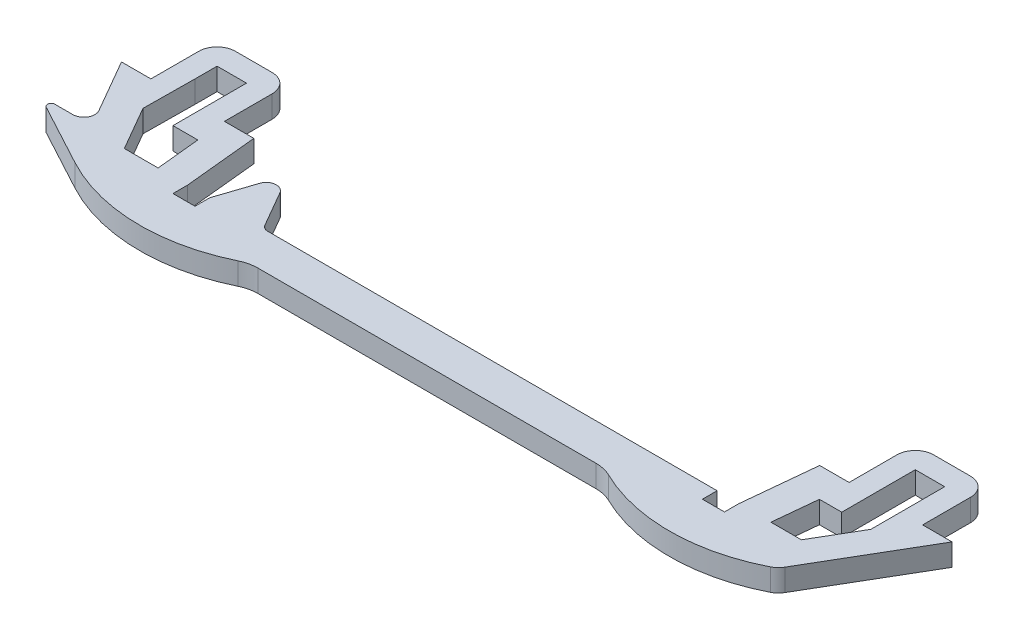
SolidWorks part; units mm, degrees
material "Custom Plastic"
ref_plane "Front Plane" through (0, 0, 0) normal (0, 0, 1) x (1, 0, 0)
ref_plane "Top Plane" through (0, 0, 0) normal (0, 1, 0) x (1, 0, 0)
ref_plane "Right Plane" through (0, 0, 0) normal (1, 0, 0) x (0, 0, -1)
sketch "Sketch1" plane through (0, 0, 0) normal (0, 1, 0) x (1, 0, 0)
  line L0 (-62.4186, -47.1375) -> (-58.4186, -47.1375)
  line L1 (-58.4186, -47.1375) -> (-58.4186, -38.1375)
  line L2 (-58.4186, -38.1375) -> (-48.4186, -38.1375)
  line L3 (-48.4186, -38.1375) -> (-48.4186, -47.1375)
  line L4 (-48.4186, -47.1375) -> (-44.4186, -47.1375)
  line L5 (-44.4186, -47.1375) -> (-43.4188, -57.135)
  line L7 (31.5814, -57.1876) -> (32.5814, -47.1902)
  line L8 (32.5814, -47.1902) -> (36.5814, -47.1902)
  line L9 (36.5814, -47.1902) -> (36.5814, -38.1902)
  line L10 (36.5814, -38.1902) -> (46.5814, -38.1902)
  line L11 (46.5814, -38.1902) -> (46.5814, -47.1902)
  line L12 (46.5814, -47.1902) -> (50.5814, -47.1902)
  line L13 (50.5814, -47.1902) -> (41.8306, -62.1375)
  line L15 (-58.2259, -54.3993) -> (-62.4186, -47.1375)
  line L16 (36.5478, -51.1902) -> (39.5814, -51.1902)
  line L17 (-55.4186, -41.1375) -> (-51.4186, -41.1375)
  line L18 (-55.4186, -41.1375) -> (-55.4186, -44.1379)
  line L20 (-51.4186, -41.1375) -> (-51.4186, -44.1375)
  line L21 (39.5814, -41.1902) -> (43.5814, -41.1902)
  line L22 (39.5814, -41.1902) -> (39.5814, -44.1902)
  line L24 (43.5814, -41.1902) -> (43.5814, -44.2297)
  line L25 (43.5814, -51.2297) -> (40.0934, -57.1876)
  line L26 (40.0934, -57.1876) -> (35.9479, -57.1876)
  line L27 (35.9479, -57.1876) -> (36.5478, -51.1902)
  line L28 (-51.4186, -51.1375) -> (-48.0385, -51.1375)
  line L29 (-48.0385, -51.1375) -> (-47.4385, -57.1375)
  line L30 (-47.4385, -57.1375) -> (-52.0263, -57.1375)
  line L31 (-52.0263, -57.1375) -> (-55.4904, -51.1375)
  line L32 (28.5814, -57.1375) -> (28.5814, -59.1375)
  line L33 (28.5814, -47.1587) -> (28.5814, -62.1587) construction
  line L34 (28.5814, -59.1375) -> (31.5814, -59.1375)
  line L35 (31.5814, -59.1375) -> (31.5814, -57.1876)
  line L36 (31.5814, -62.1587) -> (31.5814, -47.1587) construction
  line L38 (-43.4188, -57.135) -> (-43.4188, -59.1375)
  line L39 (-43.4188, -59.1375) -> (-40.4188, -59.1375)
  line L40 (-40.4188, -59.1375) -> (-40.4188, -57.1375)
  line L41 (-33.1369, -57.1375) -> (28.5814, -57.1375)
  line L42 (-33.1369, -57.1375) -> (-36.236, -51.7698)
  line L43 (43.5814, -44.2297) -> (43.5814, -51.2297)
  line L44 (-38.7227, -52.0235) -> (-40.4188, -57.1375)
  line L45 (39.5814, -44.1902) -> (39.5814, -51.1902)
  line L46 (-55.4186, -44.1379) -> (-55.4904, -51.1375)
  line L47 (-51.4186, -44.1375) -> (-51.4186, -51.1375)
  line L48 (-53.7583, -62.1375) -> (-62.2024, -57.5896)
  line L49 (-61.9653, -56.6493) -> (-59.525, -56.6493)
  line L50 (30.0814, -59.1375) -> (30.0814, -65.1375) construction
  line L51 (18.3323, -62.1375) -> (-30.0793, -62.1375)
  line L52 (-41.9188, -59.1375) -> (-41.9188, -65.1375) construction
  arc A0 (-38.7227, -52.0235) -> (-36.236, -51.7698) centre (-37.4224, -52.4548) cw
  arc A1 (-59.525, -56.6493) -> (-58.2259, -54.3993) centre (-59.525, -55.1493) ccw
  arc A2 (-62.2024, -57.5896) -> (-61.9653, -56.6493) centre (-61.9653, -57.1493) cw
  arc A3 (41.8306, -62.1375) -> (18.3323, -62.1375) centre (30.0814, -40.6304) cw
  arc A4 (-53.7583, -62.1375) -> (-30.0793, -62.1375) centre (-41.9188, -40.2752) ccw
  point P58 (30.0814, -59.1375)
  point P61 (0, 0)
  point P62 (-41.9188, -59.1375)
  point P65 (0, 0)
  dimension "D6" = 0.5
  dimension "D5" = 1.5
  dimension "D2" = 4
  dimension "D3" = 9
  dimension "D4" = 3
  dimension "D7" = 6
  dimension "D8" = 10
  dimension "D9" = 85
  dimension "D10" = 3
  dimension "D11" = 95.5889
  dimension "D12" = 3
  dimension "D13" = 3
  dimension "D14" = 3
  dimension "D15" = 3
  dimension "D16" = 14.9473
  dimension "D17" = 4
  dimension "D18" = 4
  dimension "D19" = 4
  dimension "D20" = 4
  dimension "D21" = 4
  dimension "D22" = 7.2618
  dimension "D23" = 2
  dimension "D24" = 3
  dimension "D25" = 2.4403
  dimension "D26" = 4.548
  dimension "D27" = 9.9975
  dimension "D28" = 0.9997
  dimension "D29" = 1
  dimension "D30" = 11.9473
  dimension "D31" = 4.6827
  dimension "D32" = 120
  dimension "D33" = 2.9964
  dimension "D34" = 5.114
  dimension "D35" = 4
  dimension "D36" = 4.5877
  dimension "D37" = 7
  dimension "D38" = 7
  dimension "D39" = 2
  dimension "D40" = 6
extrude "Boss-Extrude1" add sketch "Sketch1" along normal blind 3
fillet "Fillet2" radius 2.5 4 edges at (46.5814, 1.5, 38.1902) (36.5814, 1.5, 38.1902) (-58.4186, 1.5, 38.1375) (-48.4186, 1.5, 38.1375)
fillet "Fillet3" radius 1 1 edges at (-33.1369, 1.5, 57.1375)
fillet "Fillet5" radius 2.5 2 edges at (-53.7583, 1.5, 62.1375) (41.8306, 1.5, 62.1375)
fillet "Fillet6" radius 5 2 edges at (18.3323, 1.5, 62.1375) (-30.0793, 1.5, 62.1375)
